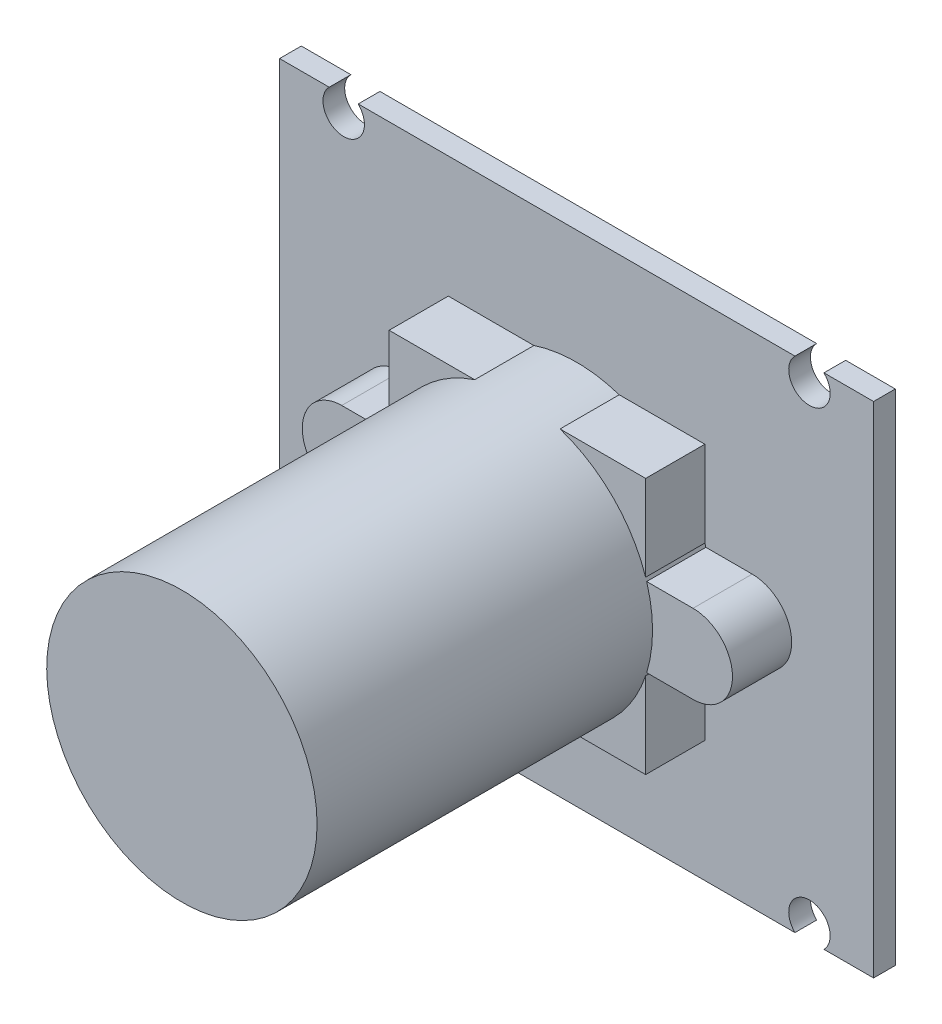
SolidWorks part; units mm, degrees
ref_plane "Front Plane" through (0, 0, 0) normal (0, 0, 1) x (1, 0, 0)
ref_plane "Top Plane" through (0, 0, 0) normal (0, 1, 0) x (1, 0, 0)
ref_plane "Right Plane" through (0, 0, 0) normal (1, 0, 0) x (0, 0, -1)
sketch "Sketch1" plane through (0, 0, 0) normal (0, 0, 1) x (1, 0, 0)
  line L1 (-15.05, -12.65) -> (15.05, -12.65)
  line L2 (-15.05, -12.65) -> (-15.05, 12.65)
  line L3 (-15.05, 12.65) -> (15.05, 12.65)
  line L4 (15.05, -12.65) -> (15.05, 12.65)
  line L5 (-15.05, -12.65) -> (15.05, 12.65) construction
  line L6 (-15.05, 12.65) -> (15.05, -12.65) construction
  point P0 (0, 0)
  dimension "D1" = 25.3
  dimension "D2" = 30.1
extrude "Boss-Extrude1" add sketch "Sketch1" along normal blind 1.1
sketch "Sketch2" plane through (0, 0, 1.1) normal (0, 0, 1) x (1, 0, 0)
  line L0 (-1000, 0) -> (49000, 0) construction
  line L1 (0, -1000) -> (0, 49000) construction
  circle A0 centre (-11.8, 11.9) radius 1.05
  circle A1 centre (11.8, 11.9) radius 1.05
  circle A2 centre (11.8, -11.9) radius 1.05
  circle A3 centre (-11.8, -11.9) radius 1.05
  dimension "D1" = 2.1
  dimension "D2" = 2.1
  dimension "D3" = 2.1
  dimension "D4" = 2.1
  dimension "D5" = 11.8
  dimension "D6" = 11.8
  dimension "D7" = 11.8
  dimension "D8" = 11.8
  dimension "D9" = 11.9
  dimension "D10" = 11.9
  dimension "D11" = 11.9
  dimension "D12" = 11.9
extrude "Cut-Extrude1" cut sketch "Sketch2" against normal through all
sketch "Sketch3" plane through (0, 0, 1.1) normal (0, 0, 1) x (1, 0, 0)
  line L1 (-6.5, -6.5) -> (6.5, -6.5)
  line L2 (-6.5, -6.5) -> (-6.5, 6.5)
  line L3 (-6.5, 6.5) -> (6.5, 6.5)
  line L4 (6.5, -6.5) -> (6.5, 6.5)
  line L5 (-6.5, -6.5) -> (6.5, 6.5) construction
  line L6 (-6.5, 6.5) -> (6.5, -6.5) construction
  point P0 (0, 0)
  dimension "D1" = 13
  dimension "D2" = 13
extrude "Boss-Extrude2" add sketch "Sketch3" along normal blind 3
sketch "Sketch4" plane through (0, 0, 1.1) normal (0, 0, 1) x (1, 0, 0)
  line L0 (-8.9, 2) -> (8.9, 2)
  line L1 (-8.9, -2) -> (8.9, -2)
  line L2 (-1000, 0) -> (49000, 0) construction
  arc A0 (-8.9, 2) -> (-8.9, -2) centre (-8.9, 0) ccw
  arc A1 (8.9, -2) -> (8.9, 2) centre (8.9, 0) ccw
  dimension "D1" = 4
  dimension "D2" = 4
  dimension "D3" = 8.9
  dimension "D4" = 8.9
extrude "Boss-Extrude3" add sketch "Sketch4" along normal blind 3
sketch "Sketch5" plane through (0, 0, 1.1) normal (0, 0, 1) x (1, 0, 0)
  circle A0 centre (0, 0) radius 6.85
  dimension "D1" = 13.7
extrude "Boss-Extrude4" add sketch "Sketch5" along normal blind 20
